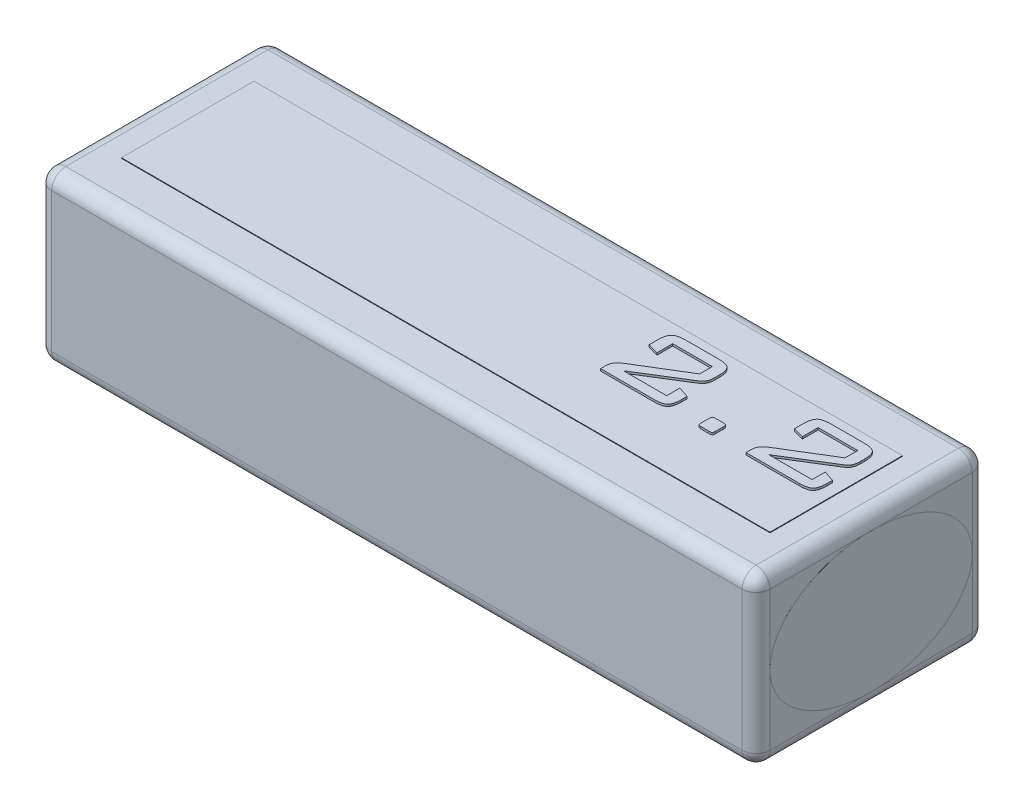
SolidWorks part; units mm, degrees
ref_plane "Plano frontal" through (0, 0, 0) normal (0, 0, 1) x (1, 0, 0)
ref_plane "Plano superior" through (0, 0, 0) normal (0, 1, 0) x (1, 0, 0)
ref_plane "Plano direito" through (0, 0, 0) normal (1, 0, 0) x (0, 0, -1)
sketch "Esboço1" plane through (0, 0, 0) normal (0, 1, 0) x (1, 0, 0)
  line L1 (-100.9348, -38.919) -> (2.0652, -38.919)
  line L2 (-100.9348, -38.919) -> (-100.9348, -5.919)
  line L3 (-100.9348, -5.919) -> (2.0652, -5.919)
  line L4 (2.0652, -38.919) -> (2.0652, -5.919)
extrude "Ressalto-extrusão1" add sketch "Esboço1" along normal blind 24
fillet "Filete1" radius 2 12 edges at (-100.9348, 12, 38.919) (-100.9348, 0, 22.419) (-100.9348, 24, 22.419) (-100.9348, 12, 5.919) (-49.4348, 24, 38.919) (-49.4348, 0, 38.919) (-49.4348, 0, 5.919) (-49.4348, 24, 5.919) (2.0652, 0, 22.419) (2.0652, 12, 38.919) (2.0652, 24, 22.419) (2.0652, 12, 5.919)
sketch "Esboço4" plane through (2.0652, 0, 0) normal (1, 0, 0) x (0, 0, -1)
  line L0 (-7.919, 22) -> (-36.919, 22) construction
  line L1 (-7.919, 2) -> (-7.919, 22) construction
  line L2 (-36.919, 2) -> (-7.919, 2) construction
  line L3 (-36.919, 22) -> (-36.919, 2) construction
  ellipse E0 centre (-22.419, 12) end of major axis (-7.919, 12) minor radius 10
  point P16 (-36.919, 12)
  dimension "D1" = 0
  dimension "D2" = 0
  dimension "D3" = 0
  dimension "D4" = 0
extrude "Ressalto-extrusão3" add sketch "Esboço4" along normal blind 0.001 separate body
sketch "Esboço5" plane through (-100.9348, 0, 0) normal (-1, 0, 0) x (0, 0, 1)
  line L0 (36.919, 2) -> (36.919, 22) construction
  line L1 (36.919, 22) -> (7.919, 22) construction
  line L2 (7.919, 22) -> (7.919, 2) construction
  line L3 (7.919, 2) -> (36.919, 2) construction
  ellipse E0 centre (22.419, 12) end of major axis (7.919, 12.4932) minor radius 10.0058
  dimension "D1" = 0
  dimension "D2" = 0
  dimension "D3" = 0
  dimension "D4" = 0
extrude "Ressalto-extrusão4" add sketch "Esboço5" along normal blind 0.001 separate body
sketch "Esboço6" plane through (0, 24, 0) normal (0, 1, 0) x (1, 0, 0)
  line L0 (-98.9348, -7.919) -> (-98.9348, -36.919) construction
  line L1 (-95.9348, -12.919) -> (-2.9348, -12.919)
  line L2 (-95.9348, -12.919) -> (-95.9348, -31.919)
  line L3 (-95.9348, -31.919) -> (-2.9348, -31.919)
  line L4 (-2.9348, -12.919) -> (-2.9348, -31.919)
  line L5 (0.0652, -36.919) -> (0.0652, -7.919) construction
  line L6 (0.0652, -7.919) -> (-98.9348, -7.919) construction
  line L7 (-98.9348, -36.919) -> (0.0652, -36.919) construction
  dimension "D1" = 3
  dimension "D2" = 3
  dimension "D3" = 5
  dimension "D4" = 5
extrude "Ressalto-extrusão5" add sketch "Esboço6" along normal blind 0.09 separate body
sketch "Esboço7" plane through (0, 24.09, 0) normal (0, 1, 0) x (1, 0, 0)
  text T0 "2.2" font "BankGothic Lt BT" height in points 36
extrude "Ressalto-extrusão6" add sketch "Esboço7" along normal blind 0.3 separate body
